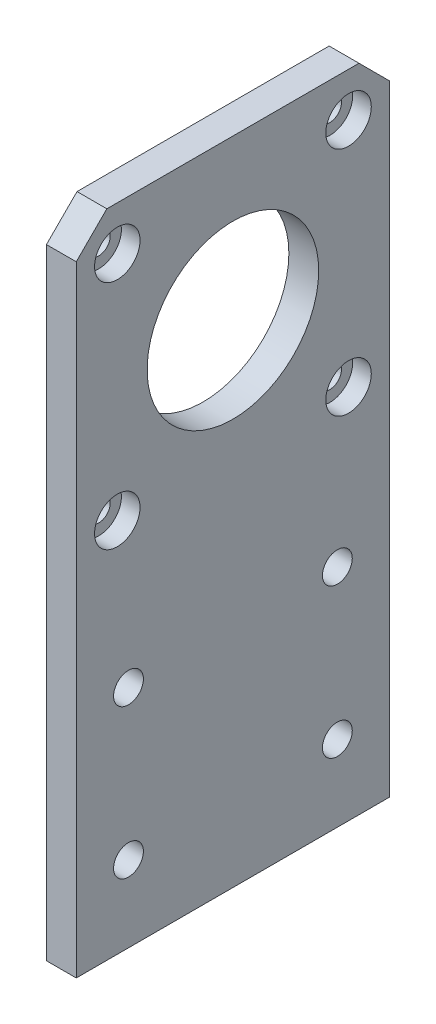
SolidWorks part; units mm, degrees
ref_plane "Alzado" through (0, 0, 0) normal (0, 0, 1) x (1, 0, 0)
ref_plane "Planta" through (0, 0, 0) normal (0, 1, 0) x (1, 0, 0)
ref_plane "Vista lateral" through (0, 0, 0) normal (1, 0, 0) x (0, 0, -1)
sketch "Croquis1" plane through (0, 0, 0) normal (1, 0, 0) x (0, 0, -1)
  line L1 (-21, -43.625) -> (21, -43.625)
  line L2 (-21, -43.625) -> (-21, 43.625)
  line L3 (-21, 43.625) -> (21, 43.625)
  line L4 (21, -43.625) -> (21, 43.625)
  line L5 (-21, -43.625) -> (21, 43.625) construction
  line L6 (-21, 43.625) -> (21, -43.625) construction
  point P0 (0, 0)
  dimension "D1" = 42
  dimension "D2" = 87.25
extrude "Saliente-Extruir1" add sketch "Croquis1" along normal blind 4
sketch "Croquis2" plane through (4, 0, 0) normal (1, 0, 0) x (0, 0, -1)
  line L0 (0, 37.745) -> (0, 43.625) construction
  line L1 (-15.5, 6.745) -> (15.5, 6.745) construction
  line L2 (-15.5, 6.745) -> (-15.5, 37.745) construction
  line L3 (-15.5, 37.745) -> (15.5, 37.745) construction
  line L4 (15.5, 6.745) -> (15.5, 37.745) construction
  line L5 (-15.5, 6.745) -> (15.5, 37.745) construction
  line L6 (-15.5, 37.745) -> (15.5, 6.745) construction
  line L8 (21, 43.625) -> (-21, 43.625) construction
  circle A0 centre (-15.5, 37.745) radius 1.55
  circle A1 centre (15.5, 37.745) radius 1.55
  circle A2 centre (15.5, 6.745) radius 1.55
  circle A3 centre (-15.5, 6.745) radius 1.55
  circle A4 centre (0, 22.245) radius 11.5
  point P8 (0, 22.245)
  dimension "D1" = 3.1
  dimension "D3" = 23
  dimension "D2" = 31
  dimension "D4" = 5.88
extrude "Cortar-Extruir1" cut sketch "Croquis2" against normal through all
sketch "Croquis3" plane through (4, 0, 0) normal (1, 0, 0) x (0, 0, -1)
  line L0 (-14, -13.405) -> (14, -13.405) construction
  line L1 (0, -13.405) -> (0, -43.625) construction
  line L2 (-21, -43.625) -> (21, -43.625) construction
  line L5 (-11.5, 22.245) -> (11.5, 22.245) construction
  line L6 (-24.7314, 13.245) -> (34.0691, 13.245) construction
  circle A0 centre (-14, -13.405) radius 2
  circle A1 centre (14, -13.405) radius 2
  circle A2 centre (0, -13.405) radius 2 construction
  circle A3 centre (-14, -33.405) radius 2
  circle A4 centre (0, -33.405) radius 2 construction
  circle A5 centre (14, -33.405) radius 2
  circle A6 centre (0, 22.245) radius 11.5 construction
  dimension "D2" = 4
  dimension "D1" = 26.65
  dimension "D3" = 28
  dimension "D5" = 20
  dimension "D7" = 9
  dimension "D4" = 2
extrude "Cortar-Extruir2" cut sketch "Croquis3" against normal through all
chamfer "Chaflán1" distance 4.1 angle 45 2 edges at (2, 43.625, -21) (2, 43.625, 21)
sketch "Croquis8" plane through (4, 0, 0) normal (1, 0, 0) x (0, 0, -1)
  circle A0 centre (15.5, 37.745) radius 3.05
  circle A1 centre (-15.5, 37.745) radius 3.05
  circle A2 centre (-15.5, 6.745) radius 3.05
  circle A3 centre (15.5, 6.745) radius 3.05
  dimension "D1" = 6.1
extrude "Cortar-Extruir3" cut sketch "Croquis8" against normal blind 2.5
